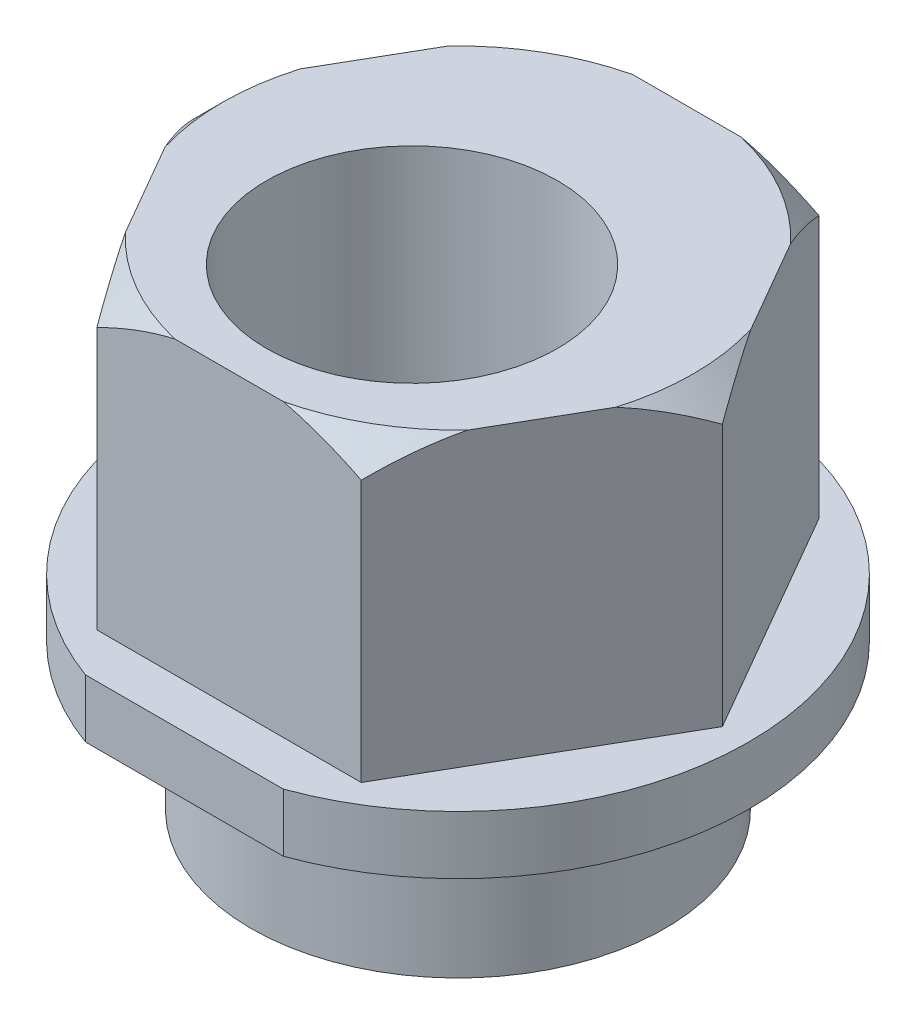
SolidWorks part; units mm, degrees
material "AISI 304"
ref_plane "Front Plane" through (0, 0, 0) normal (0, 0, 1) x (1, 0, 0)
ref_plane "Top Plane" through (0, 0, 0) normal (0, 1, 0) x (1, 0, 0)
ref_plane "Right Plane" through (0, 0, 0) normal (1, 0, 0) x (0, 0, -1)
sketch "Sketch1" plane through (0, 0, 0) normal (0, 1, 0) x (1, 0, 0)
  line L1 (4.5437, 0) -> (2.2719, 3.935)
  line L2 (2.2719, 3.935) -> (-2.2719, 3.935)
  line L3 (-2.2719, 3.935) -> (-4.5437, 0)
  line L4 (-4.5437, 0) -> (-2.2719, -3.935)
  line L5 (-2.2719, -3.935) -> (2.2719, -3.935)
  line L6 (2.2719, -3.935) -> (4.5437, 0)
  circle A0 centre (0, 0) radius 3.935 construction
  dimension "D1" = 7.87
extrude "Boss-Extrude1" add sketch "Sketch1" along normal blind 5
sketch "Sketch2" plane through (0, 0, 0) normal (0, 1, 0) x (1, 0, 0)
  circle A0 centre (0, 0) radius 5
  dimension "D1" = 10
extrude "Boss-Extrude2" add sketch "Sketch2" against normal blind 1
sketch "Sketch3" plane through (0, -1, 0) normal (0, -1, 0) x (1, 0, 0)
  circle A0 centre (0, 0) radius 3.555
  dimension "D1" = 7.11
extrude "Boss-Extrude3" add sketch "Sketch3" along normal blind 2.5
sketch "Sketch4" plane through (0, 5, 0) normal (0, 1, 0) x (1, 0, 0)
  line L0 (0, 0) -> (0, -0.79) construction
  circle A0 centre (0, -0.79) radius 2.5
  dimension "D1" = 5
  dimension "D2" = 0.79
extrude "Cut-Extrude1" cut sketch "Sketch4" against normal through all
sketch "Sketch5" plane through (0, 0, 0) normal (0, 1, 0) x (1, 0, 0)
  line L0 (-1.7, -4.7021) -> (1.7, -4.7021)
  circle A0 centre (0, 0) radius 5 construction
  arc A1 (-1.7, -4.7021) -> (1.7, -4.7021) centre (0, 0) ccw
  dimension "D1" = 3.4
extrude "Cut-Extrude2" cut sketch "Sketch5" against normal through all
sketch "Sketch6" plane through (0, 0, 0) normal (0, 0, 1) x (1, 0, 0)
  line L0 (0, 0) -> (0, 6.4706) construction
  line L1 (4.0437, 5) -> (4.5437, 5)
  line L2 (2.2719, 5) -> (4.5437, 5) construction
  line L3 (4.5437, 5) -> (4.5437, 4.5)
  line L4 (4.5437, 5) -> (4.5437, 0) construction
  line L5 (4.5437, 4.5) -> (4.0437, 5)
  dimension "D1" = 0.5
revolve "Cut-Revolve1" cut sketch "Sketch6" angle 360 about L0
move or copy body "Sólido-Mover/Copiar1" [suppressed] bodies to move or copy 106
